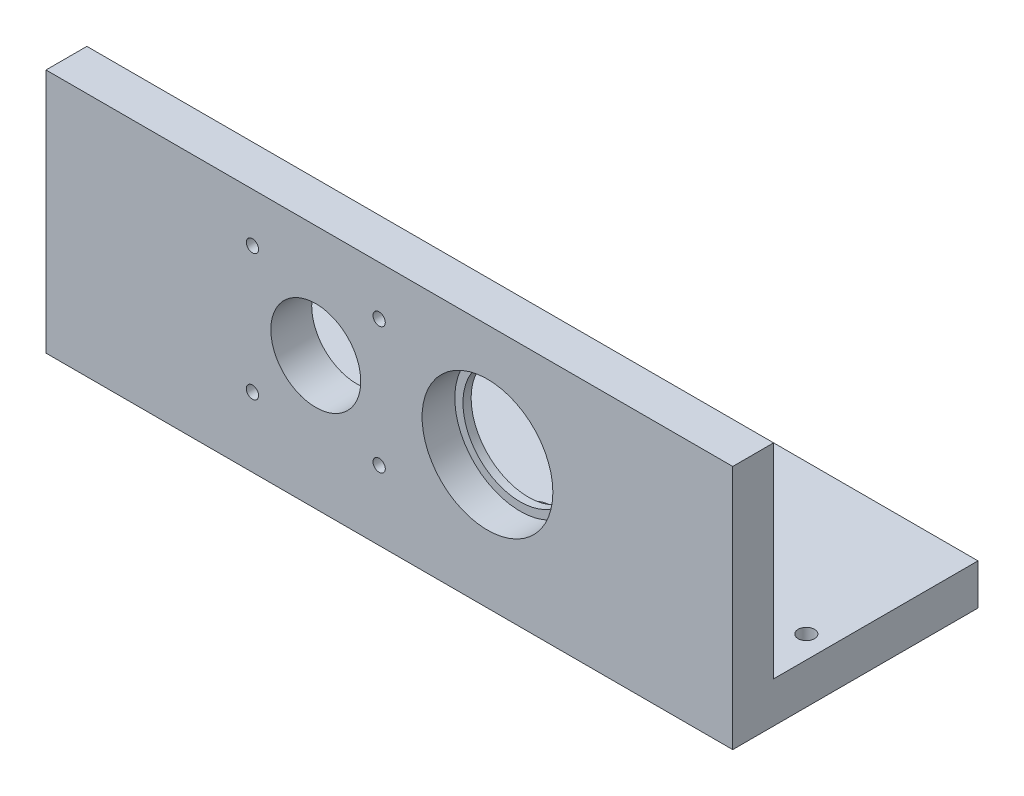
SolidWorks part; units mm, degrees
ref_plane "Ebene vorne" through (0, 0, 0) normal (0, 0, 1) x (1, 0, 0)
ref_plane "Ebene oben" through (0, 0, 0) normal (0, 1, 0) x (1, 0, 0)
ref_plane "Ebene rechts" through (0, 0, 0) normal (1, 0, 0) x (0, 0, -1)
sketch "Skizze1" plane through (0, 0, 0) normal (0, 0, 1) x (1, 0, 0)
  line L0 (0, 0) -> (0, 60)
  line L1 (0, 60) -> (168, 60)
  line L2 (168, 60) -> (168, 0)
  line L3 (168, 0) -> (0, 0)
  dimension "D1" = 168
  dimension "D2" = 60
extrude "Aufsatz-Linear austragen1" add sketch "Skizze1" along normal blind 10
sketch "Skizze2" plane through (0, 0, 10) normal (0, 0, 1) x (1, 0, 0)
  line L0 (168, 0) -> (168, 60) construction
  line L3 (0, 0) -> (168, 0) construction
  circle A0 centre (108, 32.5) radius 14
  dimension "D3" = 28
  dimension "D1" = 60
  dimension "D2" = 32.5
extrude "Schnitt-Linear austragen1" cut sketch "Skizze2" against normal blind 27
sketch "Skizze3" plane through (0, 0, 10) normal (0, 0, 1) x (1, 0, 0)
  circle A0 centre (108, 32.5) radius 16
  dimension "D1" = 32
extrude "Schnitt-Linear austragen2" cut sketch "Skizze3" against normal blind 8
sketch "Skizze4" plane through (0, 0, 0) normal (0, 0, -1) x (-1, 0, 0)
  line L0 (-168, 0) -> (-168, 60) construction
  line L1 (0, 0) -> (-168, 0) construction
  circle A0 centre (-66, 32.5009) radius 11
  dimension "D2" = 22
  dimension "D1" = 102
  dimension "D3" = 32.5009
extrude "Schnitt-Linear austragen3" cut sketch "Skizze4" against normal blind 21.6
sketch "Skizze5" plane through (0, 0, 0) normal (0, 0, -1) x (-1, 0, 0)
  line L0 (-168, 0) -> (0, 0)
  line L1 (0, 0) -> (0, 10)
  line L2 (0, 60) -> (0, 0) construction
  line L3 (0, 10) -> (-168, 10)
  line L4 (-168, 0) -> (-168, 60) construction
  line L5 (-168, 10) -> (-168, 0)
  dimension "D1" = 10
extrude "Aufsatz-Linear austragen2" add sketch "Skizze5" along normal blind 50
sketch "Skizze6" plane through (0, 10, 0) normal (0, 1, 0) x (1, 0, 0)
  line L1 (0, 50) -> (168, 50) construction
  line L3 (168, 50) -> (168, 0) construction
  line L4 (0, 50) -> (0, 0) construction
  circle A0 centre (5.5, 13.5) radius 2
  circle A1 centre (31.5, 13.5) radius 2
  circle A2 centre (162.5, 13.5) radius 2
  circle A3 centre (136.5, 13.5) radius 2
  dimension "D1" = 4
  dimension "D2" = 36.5
  dimension "D3" = 5.5
  dimension "D4" = 26
  dimension "D5" = 5.5
  dimension "D6" = 26
extrude "Schnitt-Linear austragen4" cut sketch "Skizze6" against normal blind 10
sketch "Skizze7" plane through (0, 10, 0) normal (0, 1, 0) x (1, 0, 0)
  line L0 (0, 50) -> (168, 50) construction
  line L1 (0, 50) -> (0, 0) construction
  line L2 (168, 50) -> (168, 0) construction
  circle A0 centre (104, 20) radius 2.5
  circle A1 centre (64, 20) radius 2.5
  circle A2 centre (64, 5) radius 2.5
  circle A3 centre (104, 5) radius 2.5
  dimension "D1" = 5
  dimension "D2" = 30
  dimension "D3" = 15
  dimension "D4" = 64
  dimension "D5" = 64
extrude "Schnitt-Linear austragen5" cut sketch "Skizze7" against normal blind 10
sketch "Skizze8" plane through (0, 0, 0) normal (0, 0, -1) x (-1, 0, 0)
  line L0 (0, 60) -> (0, 10) construction
  line L2 (-168, 60) -> (0, 60) construction
  circle A0 centre (-50.5, 48) radius 1.5
  circle A1 centre (-50.5, 17) radius 1.5
  circle A2 centre (-81.5, 17) radius 1.5
  circle A3 centre (-81.5, 48) radius 1.5
  dimension "D1" = 3
  dimension "D2" = 50.5
  dimension "D3" = 12
  dimension "D4" = 31
  dimension "D5" = 31
extrude "Schnitt-Linear austragen6" cut sketch "Skizze8" against normal blind 27
chamfer "Fase1" distance 2 angle 45 1 edges at (61.5, 10, -5)
chamfer "Fase2" distance 2 angle 45 1 edges at (61.5, 10, -20)
chamfer "Fase3" distance 2 angle 45 1 edges at (101.5, 10, -20)
chamfer "Fase4" distance 2 angle 45 1 edges at (101.5, 10, -5)
